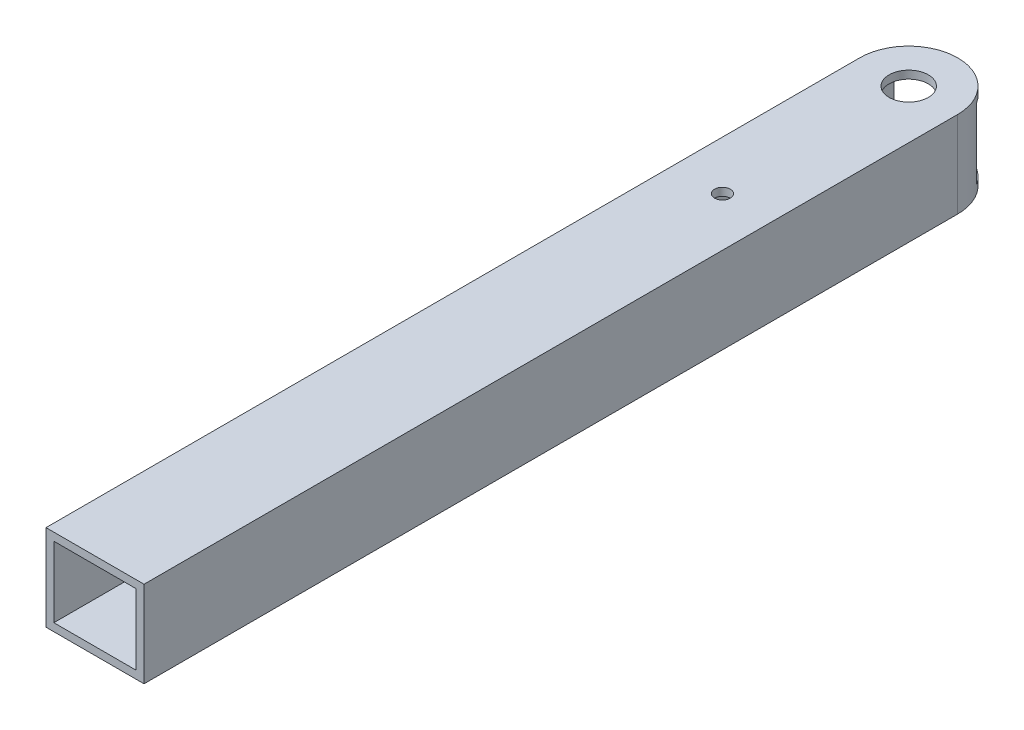
SolidWorks part; units mm, degrees
material "Thornel Mat VMA"
ref_plane "Płaszczyzna XY" through (0, 0, 0) normal (0, 0, 1) x (1, 0, 0)
ref_plane "Płaszczyzna XZ" through (0, 0, 0) normal (0, 1, 0) x (1, 0, 0)
ref_plane "Płaszczyzna YZ" through (0, 0, 0) normal (1, 0, 0) x (0, 0, -1)
sketch "Szkic1" plane through (0, 0, 0) normal (0, 0, 1) x (1, 0, 0)
  line L0 (0, 1.5) -> (0, -20.5)
  line L1 (0, -20.5) -> (25, -20.5)
  line L2 (25, -20.5) -> (25, 1.5)
  line L3 (25, 1.5) -> (0, 1.5)
  dimension "D1" = 25
  dimension "D2" = 22
  dimension "D3" = 1.5
extrude "Wyciągnięcie-cienka ścianka1" add sketch "Szkic1" along normal blind 220 thin thin type one direction reverse wall 2
sketch "Szkic2" plane through (0, -20.5, 0) normal (0, -1, 0) x (1, 0, 0)
  line L4 (0, 12.5) -> (0, 0)
  line L5 (12.5, 0) -> (25, 0)
  line L6 (0, 0) -> (25, 0) construction
  line L7 (25, 0) -> (25, 12.5)
  arc A0 (0, 12.5) -> (25, 12.5) centre (12.5, 12.5) ccw
  line M2 (0, 0) -> (25, 0)
  line M3 (25, 0) -> (25, 220)
  line M5 (0, 220) -> (0, 0)
extrude "Wytnij-wyciągnięcie1" cut sketch "Szkic2" against normal through all contours A0 M5 M2 | A0 M2 M3
sketch "Szkic3" plane through (0, -20.5, 0) normal (0, -1, 0) x (1, 0, 0)
  arc A0 (0, 12.5) -> (25, 12.5) centre (12.5, 12.5) ccw construction
  arc A1 (0, 12.5) -> (25, 12.5) centre (12.5, 12.5) ccw
  circle A2 centre (12.5, 12.5) radius 5
  dimension "D1" = 10
extrude "Wytnij-wyciągnięcie2" cut sketch "Szkic3" against normal through all contours A2
sketch "Szkic4" plane through (0, -20.5, 0) normal (0, -1, 0) x (1, 0, 0)
  line L1 (12.5, 12.5) -> (12.5, 60) construction
  circle A19 centre (12.5, 60) radius 2
  circle A25 centre (12.5, 12.5) radius 5 construction
  dimension "D1" = 47.5
  dimension "D2" = 4
extrude "Wytnij-wyciągnięcie3" cut sketch "Szkic4" against normal through all
